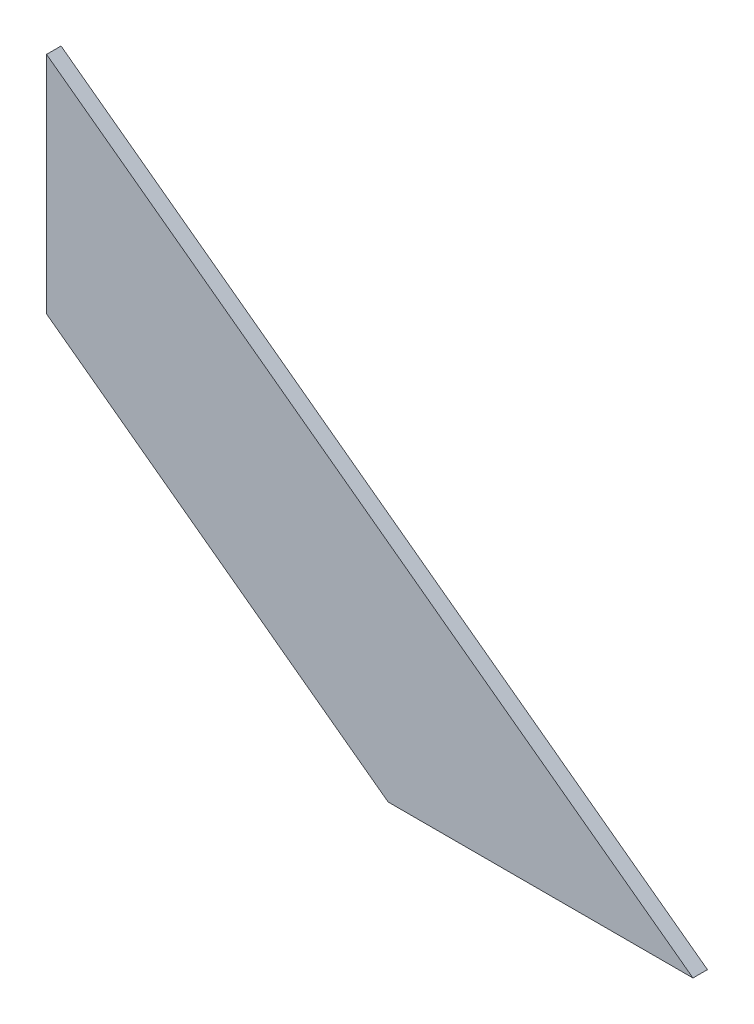
SolidWorks part; units mm, degrees
ref_plane "Front Plane" through (0, 0, 0) normal (0, 0, 1) x (1, 0, 0)
ref_plane "Top Plane" through (0, 0, 0) normal (0, 1, 0) x (1, 0, 0)
ref_plane "Right Plane" through (0, 0, 0) normal (1, 0, 0) x (0, 0, -1)
sketch "Sketch4" plane through (0, 0, 0) normal (0, 0, -1) x (-1, 0, 0)
  line L10 (471.2925, -30.2617) -> (539.3625, 19.9354)
  line L11 (539.3625, 19.9354) -> (539.3625, -3.7343)
  line L12 (539.3625, -3.7343) -> (503.3899, -30.2617)
  line L13 (503.3899, -30.2617) -> (471.2925, -30.2617)
  line L14 (564.1807, -30.2617) -> (459.4057, -30.2617) construction
  line L15 (546.4745, -26.3496) -> (546.4745, 22.1904) construction
  line L17 (446.7057, -37.2467) -> (564.1807, -37.2467) construction
  dimension "D1" = 19.05
  dimension "D2" = 7.112
  dimension "D3" = 32.0973
  dimension "D4" = 6.985
extrude "Boss-Extrude1" add sketch "Sketch4" along normal blind 1.524
